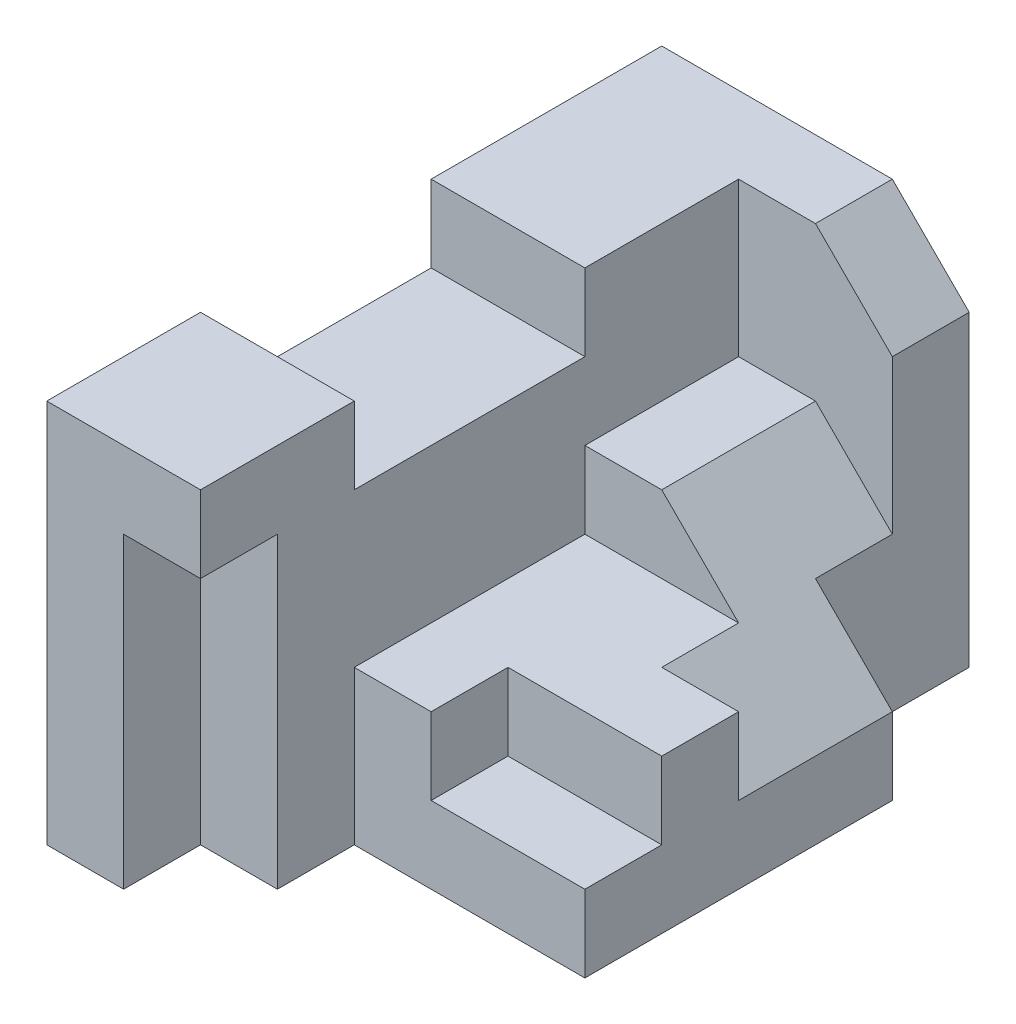
SolidWorks part; units mm, degrees
ref_plane "Front Plane" through (0, 0, 0) normal (0, 0, 1) x (1, 0, 0)
ref_plane "Top Plane" through (0, 0, 0) normal (0, 1, 0) x (1, 0, 0)
ref_plane "Right Plane" through (0, 0, 0) normal (1, 0, 0) x (0, 0, -1)
sketch "Sketch1" plane through (0, 0, 0) normal (0, 0, 1) x (1, 0, 0)
  line L1 (2.5, -2.5) -> (-2.5, -2.5)
  line L2 (2.5, -2.5) -> (2.5, 2.5)
  line L3 (2.5, 2.5) -> (-2.5, 2.5)
  line L4 (-2.5, -2.5) -> (-2.5, 2.5)
  line L5 (2.5, -2.5) -> (-2.5, 2.5) construction
  line L6 (2.5, 2.5) -> (-2.5, -2.5) construction
  point P0 (0, 0)
  dimension "D1" = 5
  dimension "D2" = 5
extrude "Boss-Extrude1" add sketch "Sketch1" along normal blind 8
sketch "Sketch2" plane through (0, 2.5, 0) normal (0, 1, 0) x (1, 0, 0)
  line L0 (-2.5, -3) -> (-0.5, -3)
  line L1 (-2.5, -8) -> (-2.5, 0) construction
  line L2 (-0.5, -3) -> (-0.5, -6)
  line L3 (-0.5, -6) -> (-2.5, -6)
  line L4 (-2.5, -6) -> (-2.5, -3)
  dimension "D1" = 3
  dimension "D2" = 3
  dimension "D3" = 2
extrude "Cut-Extrude1" cut sketch "Sketch2" against normal blind 1
sketch "Sketch4" plane through (2.5, 0, 0) normal (1, 0, 0) x (0, 0, -1)
  line L0 (-8, 1.5) -> (-7, 1.5)
  line L1 (-8, -2.5) -> (-8, 2.5) construction
  line L2 (-7, 1.5) -> (-7, -2.5)
  line L3 (-8, -2.5) -> (0, -2.5) construction
  line L4 (-7, -2.5) -> (-8, -2.5)
  line L5 (-8, -2.5) -> (-8, 1.5)
  dimension "D1" = 1
  dimension "D2" = 1
extrude "Cut-Extrude4" cut sketch "Sketch4" against normal blind 4
sketch "Sketch5" plane through (2.5, 0, 0) normal (1, 0, 0) x (0, 0, -1)
  line L0 (-7, -2.5) -> (-7, -0.5)
  line L1 (-7, -2.5) -> (-7, 1.5) construction
  line L2 (-7, -0.5) -> (-6, -0.5)
  line L3 (-6, -0.5) -> (-6, -2.5)
  line L4 (-7, -2.5) -> (0, -2.5) construction
  line L5 (-6, -2.5) -> (-7, -2.5)
  dimension "D1" = 1
  dimension "D2" = 2
extrude "Cut-Extrude5" cut sketch "Sketch5" against normal blind 3
sketch "Sketch6" plane through (2.5, 0, 0) normal (1, 0, 0) x (0, 0, -1)
  line L0 (-8, 1.5) -> (-8, 2.5)
  line L1 (-8, 2.5) -> (-1, 2.5)
  line L2 (-8, 2.5) -> (0, 2.5) construction
  line L3 (-1, 2.5) -> (-1, 0.5)
  line L4 (-1, 0.5) -> (-3, 0.5)
  line L5 (-3, 0.5) -> (-3, -0.5)
  line L6 (-3, -0.5) -> (-6, -0.5)
  line L7 (-6, -0.5) -> (-7, -0.5)
  line L10 (-7, -0.5) -> (-7, 1.5)
  line L11 (-7, 1.5) -> (-8, 1.5)
  dimension "D1" = 1
  dimension "D2" = 2
  dimension "D3" = 2
  dimension "D4" = 1
  dimension "D5" = 3
  dimension "D6" = 1
extrude "Cut-Extrude6" cut sketch "Sketch6" against normal blind 3
sketch "Sketch7" plane through (0, 0, 6) normal (0, 0, 1) x (1, 0, 0)
  line L0 (0.5, -0.5) -> (0.5, -1.5)
  line L1 (-0.5, -0.5) -> (2.5, -0.5) construction
  line L2 (0.5, -1.5) -> (2.5, -1.5)
  line L3 (2.5, -2.5) -> (2.5, -0.5) construction
  line L4 (2.5, -1.5) -> (2.5, -0.5)
  line L5 (2.5, -0.5) -> (0.5, -0.5)
  dimension "D1" = 1
  dimension "D2" = 2
extrude "Cut-Extrude7" cut sketch "Sketch7" against normal blind 1
sketch "Sketch8" plane through (0, 0, 0) normal (0, 0, -1) x (-1, 0, 0)
  line L0 (-0.5, 2.5) -> (-1.5, 1.5)
  line L1 (-2.5, 2.5) -> (2.5, 2.5) construction
  line L2 (-1.5, 1.5) -> (-1.5, -2.5)
  line L3 (2.5, -2.5) -> (-2.5, -2.5) construction
  line L4 (-1.5, -2.5) -> (-2.5, -2.5)
  line L5 (-2.5, -2.5) -> (-2.5, 2.5)
  line L6 (-2.5, 2.5) -> (-0.5, 2.5)
  dimension "D1" = 2
  dimension "D2" = 1
  dimension "D3" = 4
extrude "Cut-Extrude8" cut sketch "Sketch8" against normal blind 2
sketch "Sketch9" plane through (0, 0, 3) normal (0, 0, 1) x (1, 0, 0)
  line L0 (0.5, 0.5) -> (1.5, -0.5)
  line L1 (-0.5, 0.5) -> (2.5, 0.5) construction
  line L2 (2.5, -0.5) -> (0.5, -0.5) construction
  line L3 (1.5, -0.5) -> (2.5, -0.5)
  line L4 (2.5, -0.5) -> (2.5, 0.5)
  line L5 (2.5, 0.5) -> (0.5, 0.5)
  dimension "D1" = 1
  dimension "D2" = 2
extrude "Cut-Extrude9" cut sketch "Sketch9" against normal blind 2
sketch "Sketch10" plane through (0, 0, 2) normal (0, 0, -1) x (-1, 0, 0)
  line L0 (-1.5, -0.5) -> (-2.5, -1.5)
  line L1 (-1.5, -2.5) -> (-1.5, 1.5) construction
  line L2 (-2.5, -0.5) -> (-2.5, -2.5) construction
  line L3 (-2.5, -1.5) -> (-2.5, -0.5)
  line L4 (-2.5, -0.5) -> (-1.5, -0.5)
  dimension "D1" = 1
extrude "Cut-Extrude10" cut sketch "Sketch10" against normal blind 2
